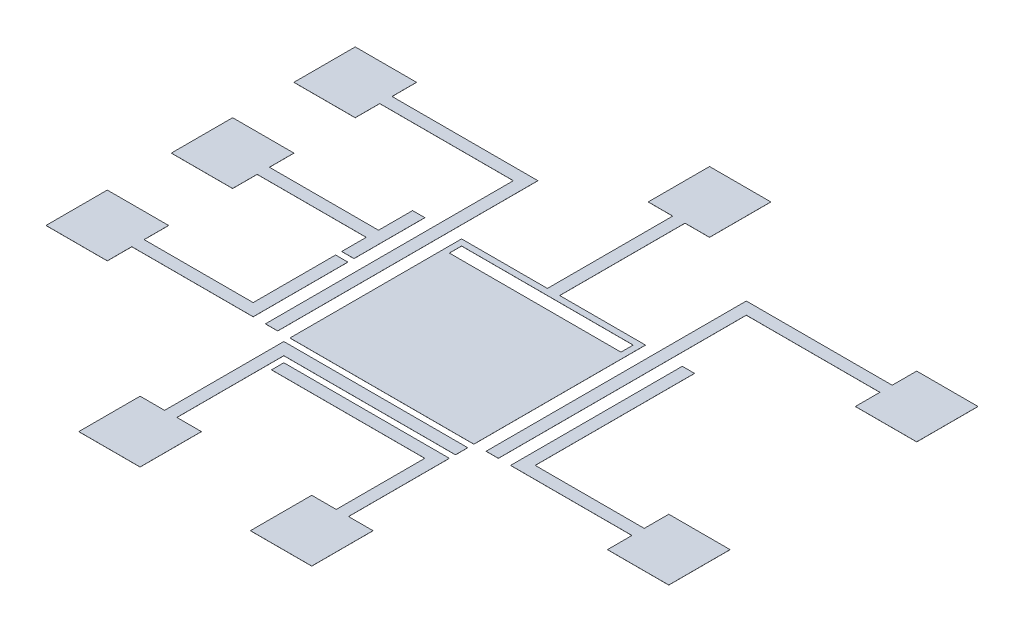
SolidWorks part; units mm, degrees
material "Copper"
ref_plane "Front Plane" through (0, 0, 0) normal (0, 0, 1) x (1, 0, 0)
ref_plane "Top Plane" through (0, 0, 0) normal (0, 1, 0) x (1, 0, 0)
ref_plane "Right Plane" through (0, 0, 0) normal (1, 0, 0) x (0, 0, -1)
sketch "Sketch1" plane through (0, 0, 0) normal (0, 1, 0) x (1, 0, 0)
  line L0 (25.9, 29.225) -> (32.9, 29.225)
  line L1 (0, 0) -> (50.8, 0)
  line L2 (0, 0) -> (0, 44.45)
  line L3 (0, 44.45) -> (50.8, 44.45)
  line L4 (50.8, 0) -> (50.8, 44.45)
  line L5 (20.4, 27.225) -> (30.4, 27.225)
  line L6 (20.4, 27.225) -> (20.4, 17.225)
  line L7 (20.4, 17.225) -> (30.4, 17.225)
  line L8 (30.4, 27.225) -> (30.4, 17.225)
  line L9 (17.9, 15.225) -> (32.9, 15.225)
  line L10 (17.9, 15.225) -> (17.9, 29.225)
  line L11 (17.9, 29.225) -> (24.9, 29.225)
  line L12 (32.9, 15.225) -> (32.9, 29.225)
  line L14 (22.9, 44.45) -> (22.9, 39.45)
  line L15 (22.9, 39.45) -> (24.9, 39.45)
  line L16 (27.9, 44.45) -> (27.9, 39.45)
  line L18 (24.9, 39.45) -> (24.9, 29.225)
  line L20 (25.9, 39.45) -> (25.9, 29.225)
  line L21 (25.9, 39.45) -> (27.9, 39.45)
  line L22 (5, 38.4487) -> (0, 38.4487)
  line L31 (5, 25.4487) -> (5, 23.4487)
  line L32 (45.8, 35.4487) -> (45.8, 33.4487)
  line L49 (18.4, 27.725) -> (32.4, 27.725)
  line L50 (18.4, 27.725) -> (18.4, 28.725)
  line L51 (18.4, 28.725) -> (32.4, 28.725)
  line L52 (32.4, 27.725) -> (32.4, 28.725)
  line L53 (50.8, 38.4487) -> (45.8, 38.4487)
  line L55 (50.8, 33.4487) -> (45.8, 33.4487)
  line L56 (45.8, 38.4487) -> (45.8, 36.4487)
  line L57 (45.8, 36.4487) -> (33.9, 36.4487)
  line L59 (45.8, 35.4487) -> (34.9, 35.4487)
  line L62 (33.9, 36.4487) -> (33.9, 15.225)
  line L63 (33.9, 15.225) -> (34.9, 15.225)
  line L64 (34.9, 35.4487) -> (34.9, 15.225)
  line L65 (45.8, 15.225) -> (45.8, 13.225)
  line L67 (35.9, 15.225) -> (35.9, 29.225)
  line L68 (35.9, 29.225) -> (36.9, 29.225)
  line L69 (36.9, 16.225) -> (36.9, 29.225)
  line L70 (35.9, 15.225) -> (45.8, 15.225)
  line L72 (36.9, 16.225) -> (45.8, 16.225)
  line L74 (50.8, 18.225) -> (45.8, 18.225)
  line L76 (50.8, 13.225) -> (45.8, 13.225)
  line L77 (45.8, 18.225) -> (45.8, 16.225)
  line L78 (5, 35.4487) -> (5, 33.4487)
  line L81 (0, 33.4487) -> (5, 33.4487)
  line L82 (5, 38.4487) -> (5, 36.4487)
  line L83 (5, 36.4487) -> (16.9, 36.4487)
  line L85 (5, 35.4487) -> (15.9, 35.4487)
  line L88 (16.9, 36.4487) -> (16.9, 15.225)
  line L89 (16.9, 15.225) -> (15.9, 15.225)
  line L90 (15.9, 35.4487) -> (15.9, 15.225)
  line L91 (0, 28.4487) -> (5, 28.4487)
  line L93 (0, 23.4487) -> (5, 23.4487)
  line L94 (5, 28.4487) -> (5, 26.4487)
  line L103 (5, 26.4487) -> (13.9, 26.4487)
  line L105 (5, 25.4487) -> (13.9, 25.4487)
  line L107 (14.9, 29.225) -> (13.9, 29.225)
  line L108 (14.9, 29.225) -> (14.9, 23.4487)
  line L109 (14.9, 23.4487) -> (13.9, 23.4487)
  line L110 (13.9, 29.225) -> (13.9, 26.4487)
  line L111 (13.9, 22.9487) -> (14.9, 22.9487)
  line L112 (13.9, 22.9487) -> (13.9, 16.225)
  line L114 (14.9, 22.9487) -> (14.9, 15.225)
  line L119 (14.9, 15.225) -> (5, 15.225)
  line L121 (13.9, 16.225) -> (5, 16.225)
  line L123 (0, 18.225) -> (5, 18.225)
  line L125 (0, 13.225) -> (5, 13.225)
  line L126 (5, 18.225) -> (5, 16.225)
  line L127 (13.9, 25.4487) -> (13.9, 23.4487)
  line L128 (5, 15.225) -> (5, 13.225)
  line L130 (18.9, 5) -> (20.9, 5)
  line L131 (17.9, 14.725) -> (32.9, 14.725)
  line L133 (18.9, 13.725) -> (32.9, 13.725)
  line L134 (32.9, 14.725) -> (32.9, 13.725)
  line L136 (17.9, 14.725) -> (17.9, 5)
  line L138 (18.9, 13.725) -> (18.9, 5)
  line L140 (15.9, 0) -> (15.9, 5)
  line L141 (15.9, 5) -> (17.9, 5)
  line L142 (20.9, 0) -> (20.9, 5)
  line L143 (19.4, 13.225) -> (32.9, 13.225)
  line L144 (19.4, 13.225) -> (19.4, 12.225)
  line L145 (19.4, 12.225) -> (31.9, 12.225)
  line L148 (32.9, 13.225) -> (32.9, 5)
  line L150 (31.9, 12.225) -> (31.9, 5)
  line L152 (29.9, 0) -> (29.9, 5)
  line L153 (29.9, 5) -> (31.9, 5)
  line L154 (34.9, 0) -> (34.9, 5)
  line L155 (32.9, 5) -> (34.9, 5)
  circle A0 centre (9.7727, 40.45) radius 2.0013
  circle A1 centre (41.5129, 40.45) radius 2
  point P13 (32.9, 22.225)
  point P22 (27.9, 41.95)
  point P77 (14.4, 23.4487)
  dimension "D17" = 4
  dimension "D19" = 4
  dimension "D20" = 4.0026
  dimension "D1" = 50.8
  dimension "D2" = 44.45
  dimension "D3" = 10
  dimension "D4" = 10
  dimension "D5" = 20.4
  dimension "D6" = 17.225
  dimension "D7" = 2.5
  dimension "D8" = 2.5
  dimension "D9" = 2
  dimension "D10" = 2
  dimension "D11" = 5
  dimension "D12" = 5
  dimension "D13" = 2
  dimension "D14" = 22.9
  dimension "D15" = 2
  dimension "D16" = 14
  dimension "D18" = 4
  dimension "D21" = 0.5
  dimension "D22" = 1
  dimension "D23" = 5
  dimension "D24" = 5
  dimension "D25" = 5
  dimension "D26" = 5
  dimension "D27" = 2
  dimension "D28" = 1
  dimension "D29" = 1
  dimension "D30" = 1
  dimension "D31" = 1
  dimension "D32" = 2
  dimension "D33" = 2
  dimension "D34" = 5
  dimension "D35" = 5
  dimension "D36" = 5
  dimension "D37" = 5
  dimension "D38" = 2
  dimension "D39" = 2
  dimension "D40" = 1
  dimension "D41" = 1
  dimension "D42" = 2
  dimension "D43" = 1
  dimension "D44" = 1
  dimension "D45" = 0.5
  dimension "D46" = 10.225
  dimension "D47" = 0.5
  dimension "D48" = 2
  dimension "D49" = 2
  dimension "D50" = 2
  dimension "D51" = 0
  dimension "D52" = 1
  dimension "D53" = 1
  dimension "D54" = 0.5
  dimension "D55" = 1
  dimension "D56" = 2
  dimension "D57" = 5
  dimension "D58" = 2
  dimension "D59" = 2
  dimension "D60" = 1
  dimension "D61" = 5
  dimension "D62" = 0.5
  dimension "D63" = 0.5
  dimension "D64" = 1
  dimension "D66" = 1
  dimension "D67" = 2
  dimension "D68" = 2
  dimension "D69" = 5
extrude "Boss-Extrude1" add sketch "Sketch1" along normal blind 0.007 contours L128 L119 L114 L111 L112 L121 L126 L123 L2 L125 | L105 L127 L109 L108 L107 L110 L103 L94 L91 L2 L93 L31 | L85 L90 L89 L88 L83 L82 L22 L2 L81 L78 | L20 L21 L16 L3 L14 L15 L18 L11 L10 L9 L12 L0 L52 L49 L50 L51 L5 L8 L7 L6 | L64 L59 L32 L55 L4 L53 L56 L57 L62 L63 | L74 L77 L72 L69 L68 L67 L70 L65 L76 L4 | L155 L148 L143 L144 L145 L150 L153 L152 L1 L154 | L1 L142 L130 L138 L133 L134 L131 L136 L141 L140 | L8 L5 L6 L7
